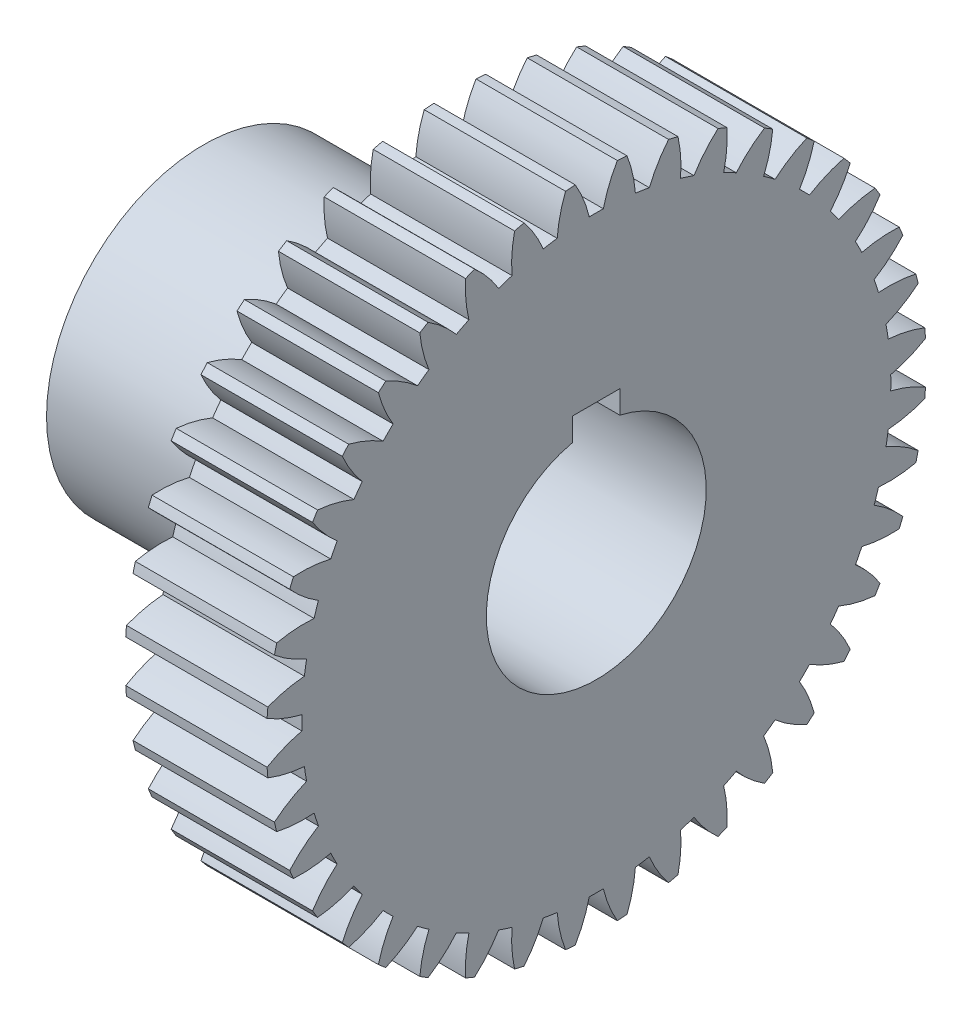
SolidWorks part; units mm, degrees
ref_plane "Plane1" through (0, 0, 0) normal (0, 0, 1) x (1, 0, 0)
ref_plane "Plane2" through (0, 0, 0) normal (0, 1, 0) x (1, 0, 0)
ref_plane "Plane3" through (0, 0, 0) normal (1, 0, 0) x (0, 0, -1)
sketch "HoldingSke" plane through (0, 0, 0) normal (0, 1, 0) x (1, 0, 0)
  line L0 (0, 0) -> (0.766, -0.6428)
  line L1 (-15, 0) -> (100, 0) construction
  line L2 (0, 0) -> (-2.1039, 2.3779)
  line L3 (0, 0) -> (-11.863, 4.5341)
  line L4 (0, 0) -> (6.6156, 5.5511)
  line L5 (0, 0) -> (-23.4238, -8.7364)
  line L6 (0, 0) -> (-7.4607, -5.0337)
  line L7 (-2.1039, 2.3779) -> (3.2774, 26.7919)
  line L8 (-76.2, 54.61) -> (-73.9, 54.61)
  line L9 (-71.009, 38.7566) -> (-53.1078, 45.2721)
  line L10 (-76.2, 71.12) -> (104.1128, 71.12)
  line L11 (0, 0) -> (-9, 0)
  line L12 (-76.2, 101.6) -> (-76.162, 101.6)
  line L13 (24.9733, 27.94) -> (52.9518, 28.4284)
  line L14 (24.9733, 27.94) -> (24.9743, 27.94)
  line L15 (24.9733, 27.94) -> (100.4006, 29.5858)
  line L16 (-63.627, -1) -> (-12.827, -1)
  circle A0 centre (0, 0) radius 7
  circle A1 centre (0, 0) radius 12.5
  circle A2 centre (0, 0) radius 12.5
  circle A3 centre (0, 0) radius 7
  dimension "MHD" = 25
  dimension "Hub_dia" = 25
  dimension "Bore" = 14
  dimension "MBD" = 14
  dimension "Num_teeth" = 40
  dimension "Pitch" = 1
  dimension "Overall_len" = 25
  dimension "Show_teeth" = 40
  dimension "Thickness" = 9
  dimension "OAL" = 25.0001
  dimension "T_dim" = 2.3
  dimension "Ap" = 20
  dimension "H" = 19.05
  dimension "Pitch_radius" = 180.3128
  dimension "Width" = 9
  dimension "Backlash" = 0.038
  dimension "Addendum_fac" = 1
  dimension "Dedendum_fac" = 1.25
  dimension "Clearance_fac" = 0.25
  dimension "Dedendum_add" = 0.001
  dimension "Module" = 1
sketch "BasProSke" plane through (0, 0, 0) normal (0, 1, 0) x (1, 0, 0)
  line L0 (-10, 0) -> (60, 0) construction
  line L1 (0, 0) -> (0, 21)
  line L2 (0, 0) -> (9, 0)
  line L3 (9, 0) -> (9, 21)
  line L4 (9, 21) -> (0, 21)
  dimension "Thickness" = 9
  dimension "Diameter" = 42
revolve "Base-Revolve" add sketch "BasProSke" angle 360 about L0
sketch "TooCutSke" plane through (0, 0, 0) normal (1, 0, 0) x (0, 0, -1)
  line L1 (0, 0) -> (0, 107) construction
  line L2 (0, 0) -> (-0.8517, 19.9819) construction
  line L3 (0, 0) -> (-3.1363, 39.8509) construction
  line L4 (-0.8517, 19.9819) -> (-1.5682, 19.9255) construction
  arc A0 (0.4487, 18.7436) -> (-0.4487, 18.7436) centre (0, 0) ccw
  arc A1 (1.3547, 20.9817) -> (-1.3547, 20.9817) centre (0, 0) ccw
  circle A2 centre (0, 0) radius 20 construction
  circle A3 centre (0, 0) radius 18.7939 construction
  arc A4 (-0.4487, 18.7436) -> (-1.3547, 20.9817) centre (-8.2322, 16.895) ccw
  arc A5 (1.3547, 20.9817) -> (0.4487, 18.7436) centre (8.2322, 16.895) ccw
  dimension "Root_dia" = 37.498
  dimension "Overcut_dia" = 42.0508
  dimension "Pitch_dia" = 40
  dimension "Base_dia" = 37.5877
  dimension "Flank_rad" = 8
  dimension "Half_ang" = 4.5
  dimension "Half_CT" = 0.7187
extrude "ToothCut" cut sketch "TooCutSke" along normal through all
fillet "Breaks" [suppressed] radius 0.02
fillet "RootFillets" [suppressed] radius 0.251
pattern_circular "TeethCuts" count 40 every 9 about axis through (-10, 0, 0) along (1, 0, 0) of "ToothCut", "RootFillets", "Breaks"
sketch "HubNeaOneSke" plane through (0, 0, 0) normal (-1, 0, 0) x (0, 0, 1)
  circle A0 centre (0, 0) radius 10
  dimension "Diameter" = 20
extrude "HubNearOne" add sketch "HubNeaOneSke" along normal blind 16.0001
sketch "HubNeaBotSke" plane through (0, 0, 0) normal (-1, 0, 0) x (0, 0, 1)
  circle A0 centre (0, 0) radius 12.5
  dimension "Diameter" = 25
extrude "HubNearBoth" [suppressed] add sketch "HubNeaBotSke" along normal blind 8
ref_plane "FarPln" through (9, 0, 0) normal (1, 0, 0) x (0, 0, -1)
sketch "HubFarSke" plane through (9, 0, 0) normal (1, 0, 0) x (0, 0, -1)
  circle A0 centre (0, 0) radius 12.5
  dimension "Diameter" = 25
extrude "HubFar" [suppressed] add sketch "HubFarSke" along normal blind 8
sketch "BorSke" plane through (0, 0, 0) normal (1, 0, 0) x (0, 0, -1)
  circle A0 centre (0, 0) radius 7
  dimension "Diameter" = 14
extrude "Bore" cut sketch "BorSke" along normal mid plane 50.0001
sketch "KeySke" plane through (0, 0, 0) normal (1, 0, 0) x (0, 0, -1)
  line L0 (-1.5, 0) -> (-1.5, 8.3)
  line L1 (-1.5, 8.3) -> (1.5, 8.3)
  line L2 (1.5, 8.3) -> (1.5, 0)
  line L3 (0, 0) -> (0, 34) construction
  line L4 (-1.5, 0) -> (1.5, 0)
  dimension "Offset" = 8.3
  dimension "Width" = 3
extrude "Keyway" cut sketch "KeySke" along normal mid plane 50.0001
pattern_circular "Keyway2" [suppressed] count 2 every 90 about axis through (-10, 0, 0) along (1, 0, 0)
equation "' \"Module@HoldingSke\" = 6.35"
equation "' \"Num_teeth@HoldingSke\" = 12"
equation "' \"Ap@HoldingSke\" =  20"
equation "' \"Ap@HoldingSke\" = 20"
equation "' \"Width@HoldingSke\" = 0.5 * 25.4"
equation "' \"Hub_dia@HoldingSke\"= 1 * 25.4"
equation "' \"Hub_dia@HoldingSke\" = 1 * 25.4"
equation "' \"Overall_len@HoldingSke\" = 1.0 * 25.4"
equation "' \"Bore@HoldingSke\" = 0.75 * 25.4"
equation "' \"T_dim@HoldingSke\" = 0.1 * 25.4"
equation "' \"Width@KeySke\" = 0.25 * 25.4"
equation "' \"Show_teeth@HoldingSke\" = 13"
equation "' \"Backlash@HoldingSke\" = 0.009 * 25.4"
equation "' \"Addendum_fac@HoldingSke\" = 1.0"
equation "' \"Dedendum_fac@HoldingSke\" = 1.25"
equation "' \"Dedendum_add@HoldingSke\" = 0.00005 * 25.4"
equation "' \"Clearance_fac@HoldingSke\" = 0.25"
equation "\"Pitch@HoldingSke\" = 1 / \"Module@HoldingSke\""
equation "\"Overcut_dia@TooCutSke\" = (\"Num_teeth@HoldingSke\" + 2 * \"Addendum_fac@HoldingSke\") / \"Pitch@HoldingSke\" + 0.002 * 25.4"
equation "\"Pitch_dia@TooCutSke\" = \"Num_teeth@HoldingSke\" / \"Pitch@HoldingSke\""
equation "\"Base_dia@TooCutSke\" = \"Num_teeth@HoldingSke\" / \"Pitch@HoldingSke\" * cos((\"Ap@HoldingSke\"  * 3.14159265 / 180))"
equation "\"Root_dia@TooCutSke\" = (\"Num_teeth@HoldingSke\" + 2) / \"Pitch@HoldingSke\" - 2 * (\"Addendum_fac@HoldingSke\" + \"Dedendum_fac@HoldingSke\") / \"Pitch@HoldingSke\" - \"Dedendum_add@HoldingSke\" * 2"
equation "\"Half_ang@TooCutSke\" = 180 / \"Num_teeth@HoldingSke\""
equation "\"Half_CT@TooCutSke\" = \"Num_teeth@HoldingSke\" / \"Pitch@HoldingSke\" * sin((3.14159265 / 2 / \"Num_teeth@HoldingSke\")) / 2 - 7 * \"Backlash@HoldingSke\" / 4"
equation "\"Flank_rad@TooCutSke\" = \"Num_teeth@HoldingSke\" / \"Pitch@HoldingSke\" / 5"
equation "\"Radius@RootFillets\" = \"Clearance_fac@HoldingSke\" / \"Pitch@HoldingSke\" + \"Dedendum_add@HoldingSke\""
equation "\"Break_rad@Breaks\" = 0.02 / \"Pitch@HoldingSke\""
equation "\"Thickness@HoldingSke\" = \"Width@HoldingSke\""
equation "\"OAL@HoldingSke\" = \"Thickness@HoldingSke\""
equation "\"MHD@HoldingSke\" = (\"Num_teeth@HoldingSke\" + 2) / \"Pitch@HoldingSke\" - 2 * (\"Addendum_fac@HoldingSke\" + \"Dedendum_fac@HoldingSke\")  / \"Pitch@HoldingSke\" - \"Dedendum_add@HoldingSke\" * 2"
equation "\"MBD@HoldingSke\" = (\"Num_teeth@HoldingSke\" + 2) / \"Pitch@HoldingSke\" - 2 * (\"Addendum_fac@HoldingSke\" + \"Dedendum_fac@HoldingSke\")  / \"Pitch@HoldingSke\" - \"Dedendum_add@HoldingSke\" * 2 - 0.002 * 25.4"
equation "\"MHD@HoldingSke\" = ((sgn( \"MHD@HoldingSke\" - \"Hub_dia@HoldingSke\" )-1)*( \"MHD@HoldingSke\" - \"Hub_dia@HoldingSke\" ))/-2+ \"Hub_dia@HoldingSke\""
equation "\"MBD@HoldingSke\" = ((sgn( \"MBD@HoldingSke\" - \"Bore@HoldingSke\" )-1)*( \"MBD@HoldingSke\" - \"Bore@HoldingSke\" ))/-2+ \"Bore@HoldingSke\""
equation "\"OAL@HoldingSke\" = ((sgn( \"OAL@HoldingSke\" - \"Overall_len@HoldingSke\" )+1)*( \"OAL@HoldingSke\" - \"Overall_len@HoldingSke\" ))/2 + \"Overall_len@HoldingSke\" + 0.000002 * 25.4"
equation "\"Num_teeth@TeethCuts\" = int( \"Show_teeth@HoldingSke\" ) + 1"
equation "\"Num_teeth@TeethCuts\" = ((sgn( \"Num_teeth@TeethCuts\" - \"Num_teeth@HoldingSke\" )-1)*( \"Num_teeth@TeethCuts\" - \"Num_teeth@HoldingSke\" ))/-2+ \"Num_teeth@HoldingSke\""
equation "\"Num_teeth@TeethCuts\" = ((sgn( \"Num_teeth@TeethCuts\" - 2.0)+1)*( \"Num_teeth@TeethCuts\" - 2.0))/2 +2.0"
equation "\"Angle@TeethCuts\" = 360.0 / \"Num_teeth@HoldingSke\""
equation "\"Diameter@BasProSke\" = (\"Num_teeth@HoldingSke\" + 2 * \"Addendum_fac@HoldingSke\") / \"Pitch@HoldingSke\""
equation "\"Thickness@BasProSke\"  = \"Thickness@HoldingSke\""
equation "' \"Fillet_rad@BasProSke\" =  \"Thickness@HoldingSke\" * 0.05"
equation "' \"Fillet_rad@BasProSke\" = \"Thickness@HoldingSke\" * 0.05"
equation "\"MHD@HoldingSke\" = ((sgn( \"MHD@HoldingSke\" - \"Root_dia@TooCutSke\" )-1)*( \"MHD@HoldingSke\" - \"Root_dia@TooCutSke\" ))/-2+ \"Root_dia@TooCutSke\""
equation "\"Diameter@HubNeaOneSke\"=20"
equation "\"Length@HubNearOne\" = \"OAL@HoldingSke\" - \"Thickness@BasProSke\""
equation "\"Diameter@HubNeaBotSke\" = \"MHD@HoldingSke\""
equation "\"Length@HubNearBoth\" = ( \"OAL@HoldingSke\" - \"Thickness@BasProSke\" ) / 2.0"
equation "\"Thickness@FarPln\" = \"Thickness@BasProSke\""
equation "\"Diameter@HubFarSke\" = \"MHD@HoldingSke\""
equation "\"Length@HubFar\" = ( \"OAL@HoldingSke\" - \"Thickness@BasProSke\" ) / 2.0"
equation "\"Diameter@BorSke\" = \"MBD@HoldingSke\""
equation "\"D1@Bore\" = \"OAL@HoldingSke\" * 2.0"
equation "\"D1@Keyway\" = \"OAL@HoldingSke\" * 2.0"
equation "\"Offset@KeySke\"=8.3"
